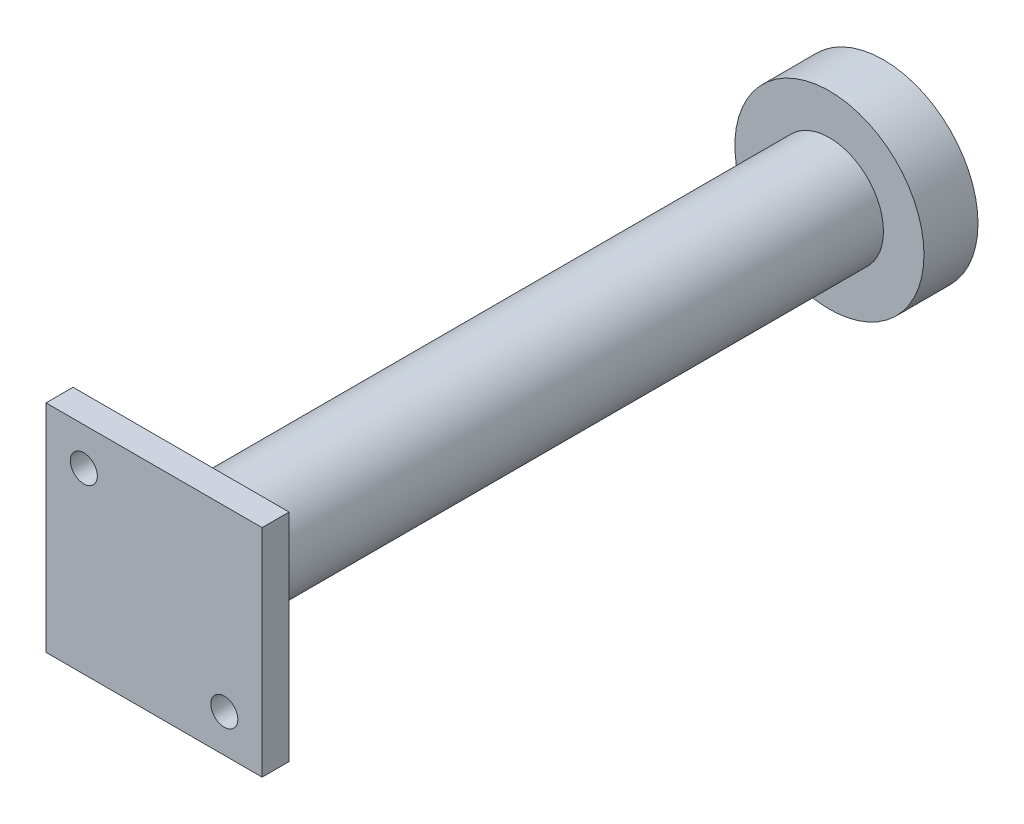
SolidWorks part; units mm, degrees
ref_plane "Plan de face" through (0, 0, 0) normal (0, 0, 1) x (1, 0, 0)
ref_plane "Plan de dessus" through (0, 0, 0) normal (0, 1, 0) x (1, 0, 0)
ref_plane "Plan de droite" through (0, 0, 0) normal (1, 0, 0) x (0, 0, -1)
sketch "Esquisse1" plane through (0, 0, 0) normal (0, 0, 1) x (1, 0, 0)
  circle A0 centre (0, 0) radius 10
  dimension "D1" = 20
extrude "Boss.-Extru.1" add sketch "Esquisse1" along normal blind 100
sketch "Esquisse2" plane through (0, 0, 0) normal (0, 0, -1) x (-1, 0, 0)
  circle A0 centre (0, 0) radius 17.5
  dimension "D1" = 35
extrude "Boss.-Extru.2" add sketch "Esquisse2" along normal blind 30
sketch "Esquisse3" plane through (0, 0, 100) normal (0, 0, 1) x (1, 0, 0)
  line L1 (-20, 20) -> (20, 20)
  line L2 (-20, 20) -> (-20, -20)
  line L3 (-20, -20) -> (20, -20)
  line L4 (20, 20) -> (20, -20)
  dimension "D1" = 40
  dimension "D2" = 40
  dimension "D3" = 20
  dimension "D4" = 20
extrude "Boss.-Extru.3" add sketch "Esquisse3" along normal blind 5
sketch "Esquisse4" plane through (0, 0, 105) normal (0, 0, 1) x (1, 0, 0)
  line L0 (-20, 20) -> (-20, -20) construction
  line L2 (20, 20) -> (-20, 20) construction
  line L3 (20, -20) -> (20, 20) construction
  line L4 (-20, -20) -> (20, -20) construction
  circle A0 centre (-13, 13) radius 2.5
  circle A1 centre (13, -13) radius 2.5
  dimension "D5" = 5
  dimension "D6" = 5
  dimension "D1" = 7
  dimension "D2" = 7
  dimension "D3" = 7
  dimension "D4" = 7
extrude "Enlèv. mat.-Extru.1" cut sketch "Esquisse4" against normal blind 5
sketch "Esquisse5" plane through (0, 0, 0) normal (0, 0, 1) x (1, 0, 0)
  circle A0 centre (0, 0) radius 10
extrude "Enlèv. mat.-Extru.3" cut sketch "Esquisse5" against normal blind 20 flip side to cut
